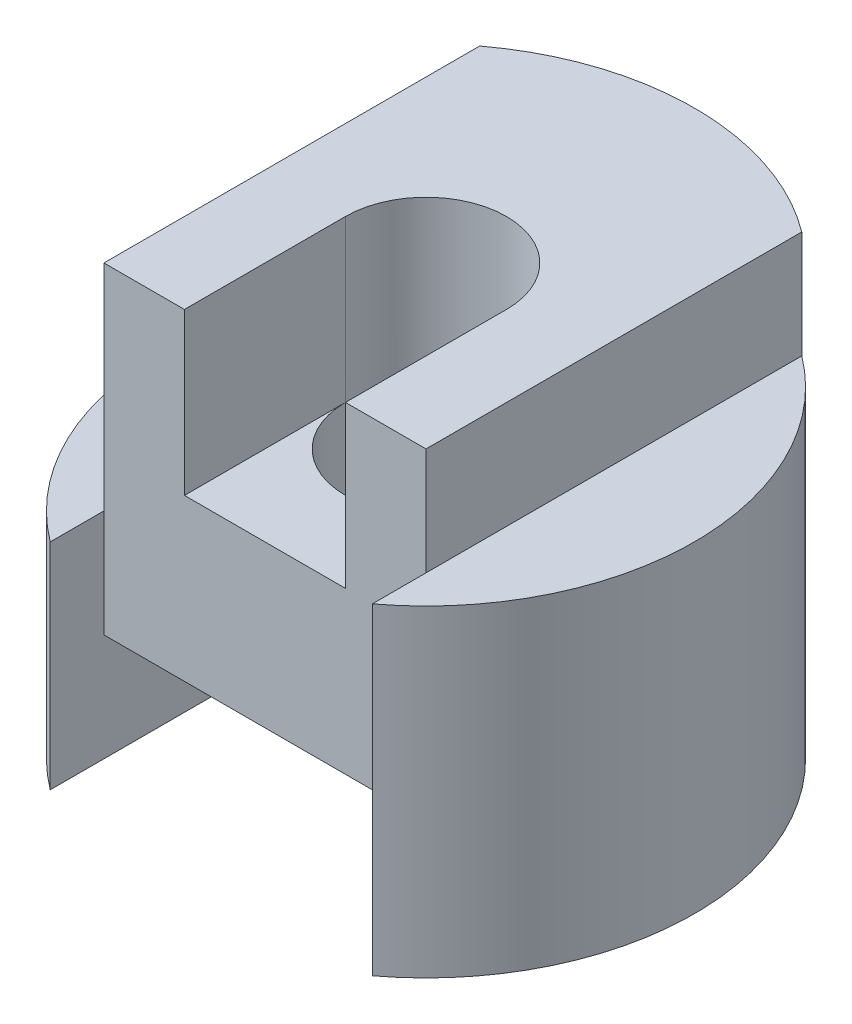
SolidWorks part; units mm, degrees
ref_plane "Front" through (0, 0, 0) normal (0, 0, 1) x (1, 0, 0)
ref_plane "Top" through (0, 0, 0) normal (0, 1, 0) x (1, 0, 0)
ref_plane "Right" through (0, 0, 0) normal (1, 0, 0) x (0, 0, -1)
sketch "Sketch1" plane through (0, 0, 0) normal (0, 1, 0) x (1, 0, 0)
  line L2 (-3, -4) -> (-3, -3)
  line L3 (-3, -3) -> (3, -3)
  line L4 (3, -4) -> (3, -3)
  arc A0 (3, -4) -> (-3, -4) centre (0, 0) ccw
  circle A1 centre (0, 0) radius 1.5
  point P8 (0, 0)
  dimension "D1" = 3
  dimension "D2" = 10
  dimension "D3" = 1
  dimension "D5" = 3
  dimension "D6" = 3
extrude "Boss-Extrude1" add sketch "Sketch1" along normal blind 8
sketch "Sketch2" plane through (0, 0, 0) normal (0, 0, 1) x (1, 0, 0)
  line L0 (3, 8) -> (3, 0) construction
  line L1 (5, 8) -> (3, 8)
  line L2 (5, 8) -> (5, 6)
  line L3 (5, 6) -> (3, 6)
  line L4 (3, 8) -> (3, 6)
  line L5 (-3, 8) -> (-3, 0) construction
  line L6 (-5, 8) -> (-3, 8)
  line L7 (-5, 8) -> (-5, 4)
  line L8 (-5, 4) -> (-3, 4)
  line L9 (-3, 8) -> (-3, 4)
  line L10 (3, 8) -> (3, 0) construction
  line L11 (-3, 0) -> (3, 0)
  line L12 (-3, 0) -> (-3, 2)
  line L13 (-3, 2) -> (3, 2)
  line L14 (3, 0) -> (3, 2)
  dimension "D1" = 2
  dimension "D2" = 4
  dimension "D3" = 2
extrude "Cut-Extrude1" cut sketch "Sketch2" against normal mid plane 18
sketch "Sketch3" plane through (0, 0, 0) normal (0, 0, 1) x (1, 0, 0)
  line L0 (1.5, 2) -> (1.5, 8) construction
  line L1 (-1.5, 8) -> (1.5, 8)
  line L2 (-1.5, 8) -> (-1.5, 5)
  line L3 (-1.5, 5) -> (1.5, 5)
  line L4 (1.5, 8) -> (1.5, 5)
  dimension "D1" = 3
extrude "Cut-Extrude2" cut sketch "Sketch3" along normal blind 18
